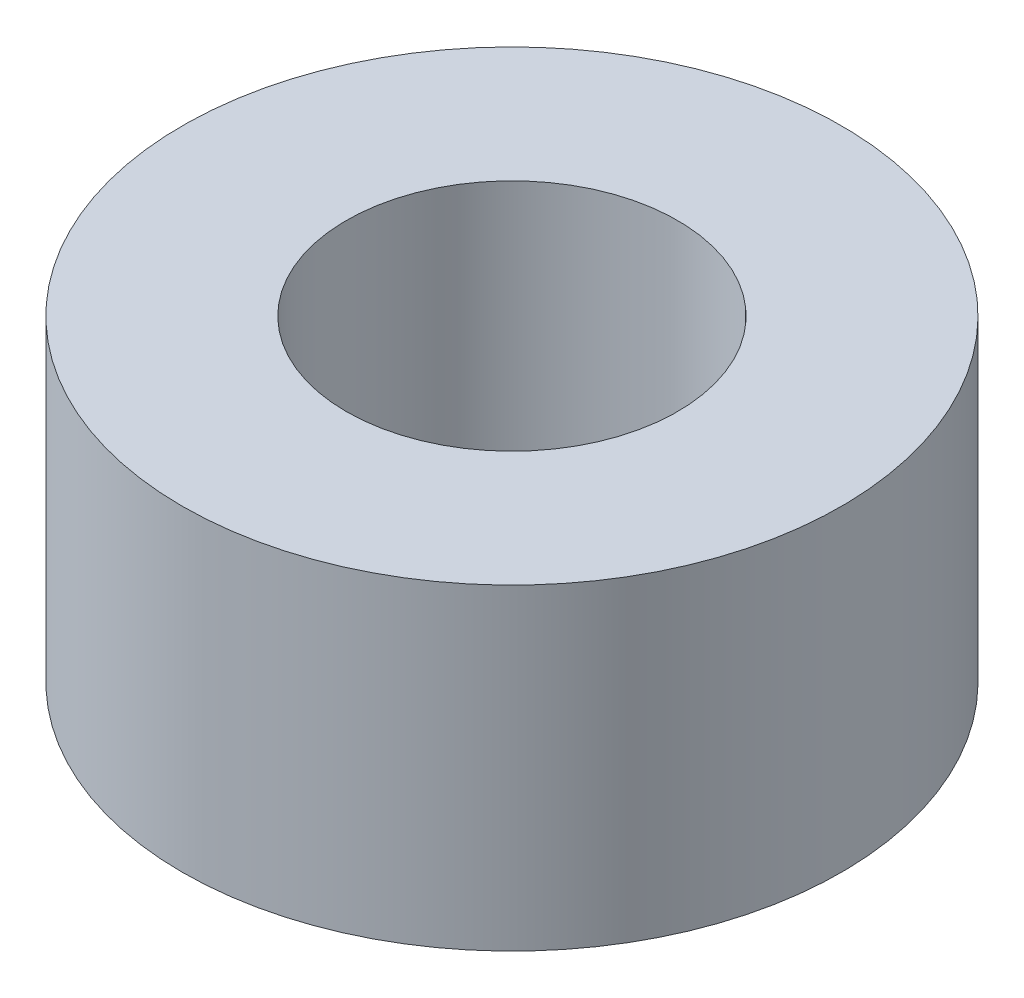
SolidWorks part; units mm, degrees
ref_plane "Front Plane" through (0, 0, 0) normal (0, 0, 1) x (1, 0, 0)
ref_plane "Top Plane" through (0, 0, 0) normal (0, 1, 0) x (1, 0, 0)
ref_plane "Right Plane" through (0, 0, 0) normal (1, 0, 0) x (0, 0, -1)
sketch "Sketch1" plane through (0, 0, 0) normal (0, 1, 0) x (1, 0, 0)
  circle A0 centre (0, 0) radius 3.015
  circle A1 centre (0, 0) radius 1.515
  dimension "D1" = 6.03
  dimension "D2" = 3.03
extrude "Boss-Extrude1" add sketch "Sketch1" along normal blind 2.9
